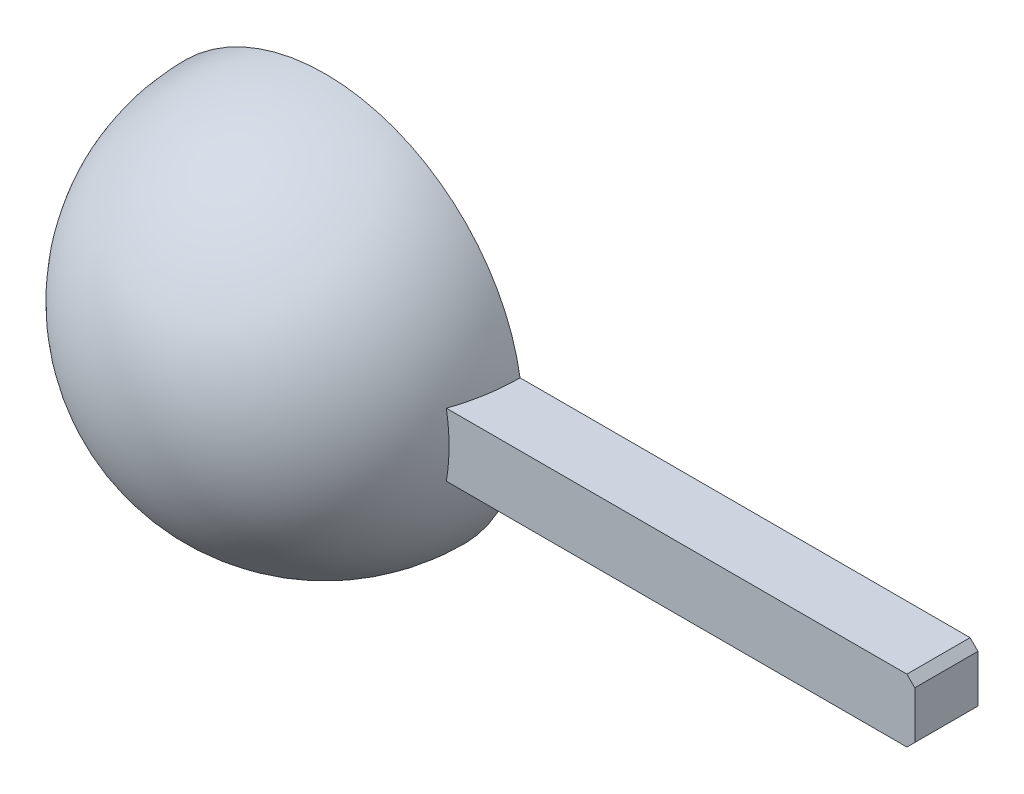
SolidWorks part; units mm, degrees
ref_plane "Plan de face" through (0, 0, 0) normal (0, 0, 1) x (1, 0, 0)
ref_plane "Plan de dessus" through (0, 0, 0) normal (0, 1, 0) x (1, 0, 0)
ref_plane "Plan de droite" through (0, 0, 0) normal (1, 0, 0) x (0, 0, -1)
sketch "Esquisse1" plane through (0, 0, 0) normal (0, 0, 1) x (1, 0, 0)
  line L0 (-25, 0) -> (25, 0)
  arc A0 (-25, 0) -> (25, 0) centre (0, 0) cw
  dimension "D1" = 25
revolve "Révolution1" add sketch "Esquisse1" angle 180 about L0
shell "Coque1" thickness 2
sketch "Esquisse2" plane through (0, 0, 0) normal (0, 0, 1) x (1, 0, 0)
  line L0 (22.6495, 4) -> (82.6495, 4)
  line L1 (82.6495, 4) -> (82.6495, -4)
  line L2 (82.6495, -4) -> (22.6495, -4)
  line L3 (22.6495, -4) -> (22.6495, 4)
  circle A0 centre (0, 0) radius 23 construction
  dimension "D1" = 4
  dimension "D2" = 4
  dimension "D3" = 60
extrude "Boss.-Extru.1" add sketch "Esquisse2" along normal blind 8 contours L2 L3 L0 L1
chamfer "Chanfrein1" distance 1 angle 45 2 edges at (82.6495, 4, 4) (82.6495, -4, 4)
